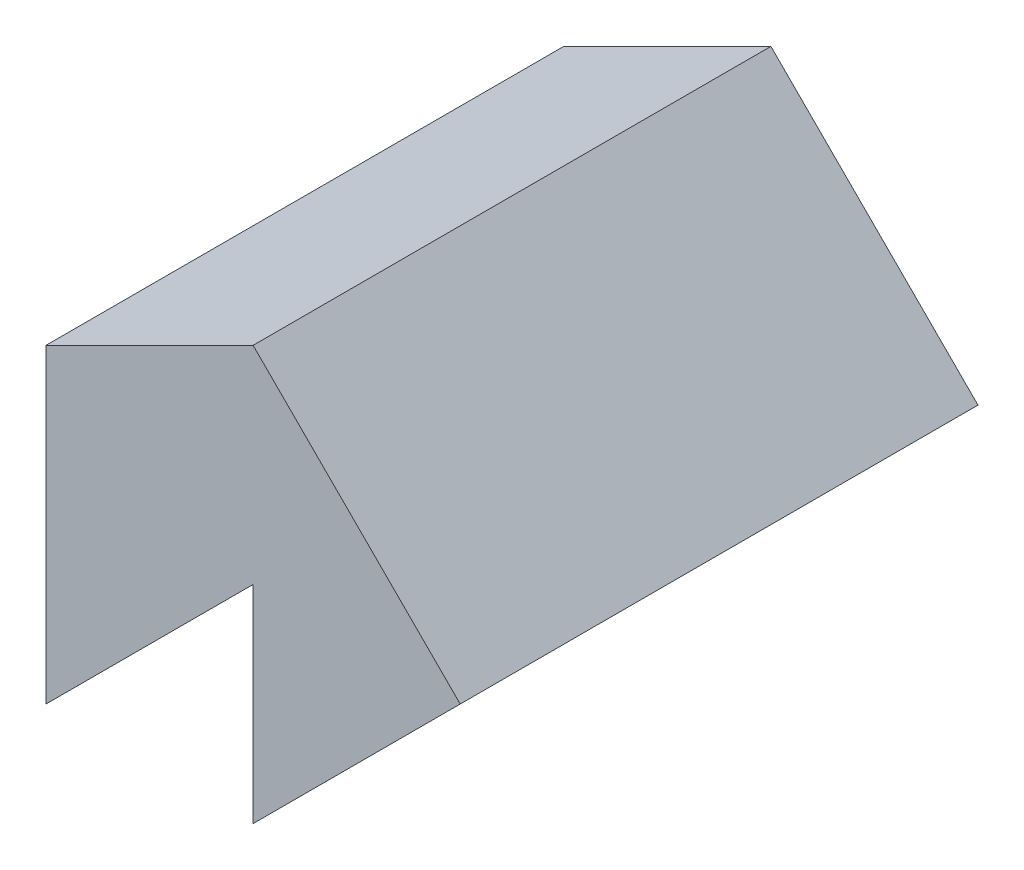
SolidWorks part; units mm, degrees
ref_plane "Front Plane" through (0, 0, 0) normal (0, 0, 1) x (1, 0, 0)
ref_plane "Top Plane" through (0, 0, 0) normal (0, 1, 0) x (1, 0, 0)
ref_plane "Right Plane" through (0, 0, 0) normal (1, 0, 0) x (0, 0, -1)
sketch "Sketch1" plane through (0, 0, 0) normal (0, 0, 1) x (1, 0, 0)
  line L0 (-10, 5) -> (0, 10)
  line L1 (0, 10) -> (10, 0)
  line L2 (10, 0) -> (0, -10)
  line L3 (0, -10) -> (0, 0)
  line L4 (0, 0) -> (-10, -10)
  line L5 (-10, -10) -> (-10, 5)
  dimension "D1" = 10
  dimension "D2" = 15
  dimension "D3" = 10
  dimension "D4" = 10
extrude "Boss-Extrude1" add sketch "Sketch1" along normal blind 25
